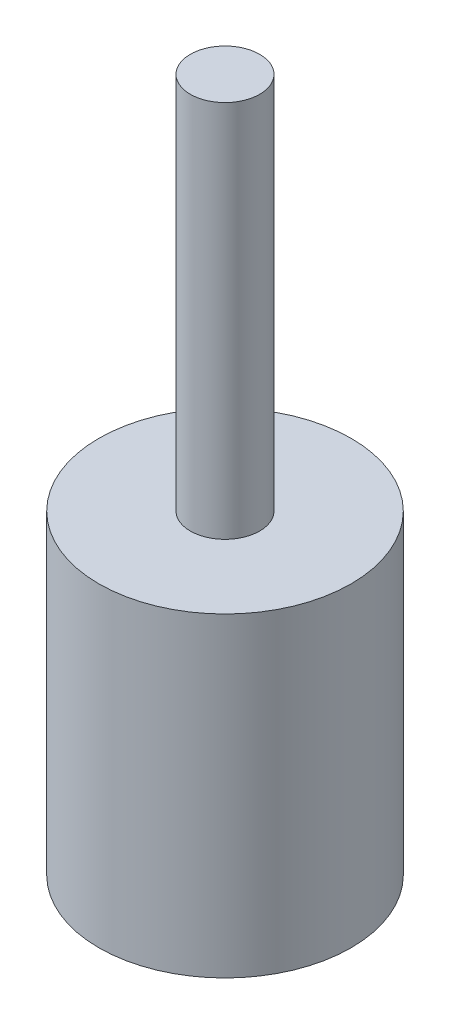
SolidWorks part; units mm, degrees
ref_plane "Plano frontal" through (0, 0, 0) normal (0, 0, 1) x (1, 0, 0)
ref_plane "Plano superior" through (0, 0, 0) normal (0, 1, 0) x (1, 0, 0)
ref_plane "Plano direito" through (0, 0, 0) normal (1, 0, 0) x (0, 0, -1)
sketch "Esboço1" plane through (0, 0, 0) normal (0, 0, 1) x (1, 0, 0)
  line L0 (0, 0) -> (0, 132.364) construction
  line L1 (0, 0) -> (79.4441, 0) construction
  line L2 (0, 100) -> (40, 100)
  line L3 (40, 100) -> (40, 0)
  line L4 (40, 0) -> (0, 0)
  line L5 (0, 0) -> (0, 100)
  dimension "D1" = 80
  dimension "D2" = 100
revolve "Revolução1" add sketch "Esboço1" angle 360 about L0
sketch "Esboço2" plane through (0, 0, 0) normal (0, 0, 1) x (1, 0, 0)
  line L0 (0, 100) -> (0, 250.3148) construction
  line L1 (40, 100) -> (-40, 100) construction
  line L2 (0, 220) -> (11, 220)
  line L3 (11, 220) -> (11, 100)
  line L4 (11, 100) -> (0, 100)
  line L5 (0, 100) -> (0, 220)
  dimension "D1" = 22
  dimension "D2" = 120
revolve "Revolução2" add sketch "Esboço2" angle 360 about L0
